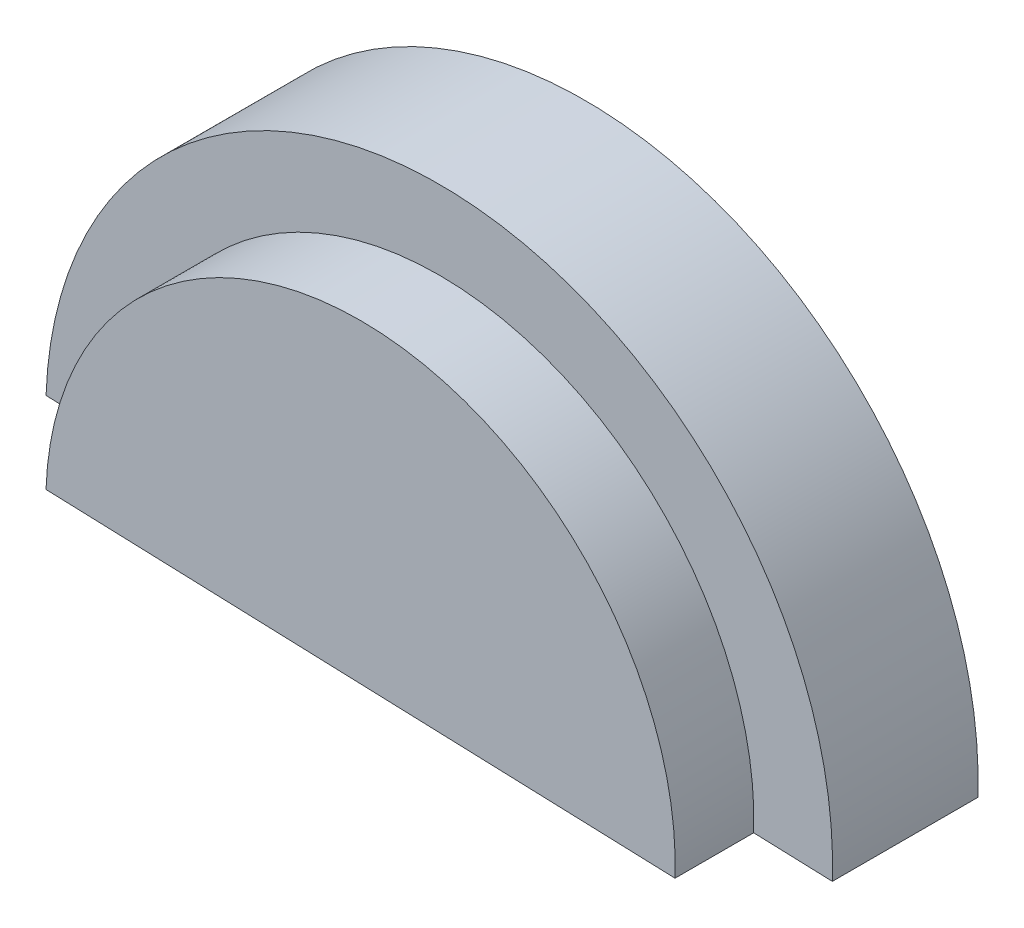
SolidWorks part; units mm, degrees
ref_plane "Plan de face" through (0, 0, 0) normal (0, 0, 1) x (1, 0, 0)
ref_plane "Plan de dessus" through (0, 0, 0) normal (0, 1, 0) x (1, 0, 0)
ref_plane "Plan de droite" through (0, 0, 0) normal (1, 0, 0) x (0, 0, -1)
sketch "Esquisse1" plane through (0, 0, 0) normal (0, 0, 1) x (1, 0, 0)
  line L0 (0, 0) -> (999.3804, -35.1975)
  arc A0 (0, 0) -> (999.3804, -35.1975) centre (499.6902, -17.5988) cw
  dimension "D1" = 500
extrude "Boss.-Extru.1" add sketch "Esquisse1" along normal blind 185
sketch "Esquisse3" plane through (0, 0, 185) normal (0, 0, 1) x (1, 0, 0)
  line L0 (0, 0) -> (999.3804, -35.1975) construction
  line L1 (99.938, -3.5198) -> (899.4423, -31.6778)
  arc A0 (99.938, -3.5198) -> (899.4423, -31.6778) centre (499.6902, -17.5988) cw
  dimension "D1" = 400
extrude "Boss.-Extru.2" add sketch "Esquisse3" along normal blind 100
